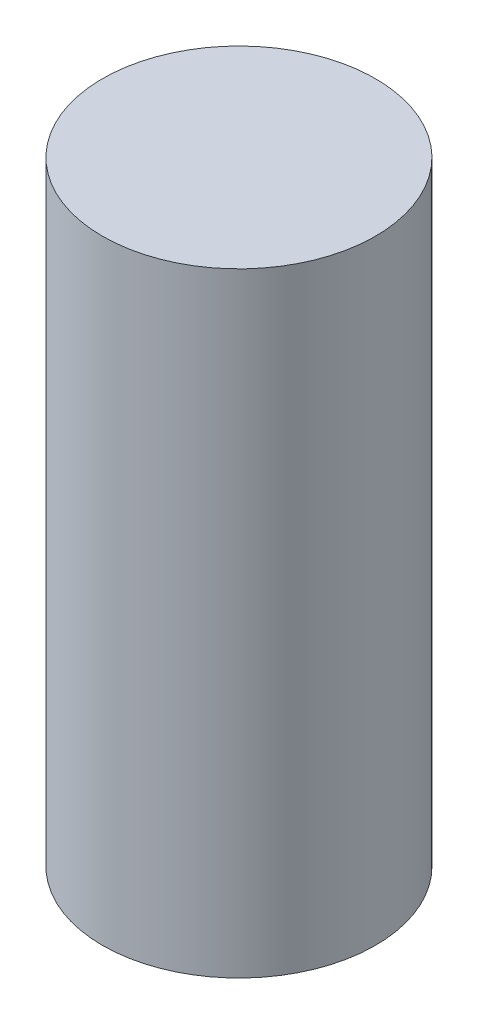
SolidWorks part; units mm, degrees
ref_plane "Front Plane" through (0, 0, 0) normal (0, 0, 1) x (1, 0, 0)
ref_plane "Top Plane" through (0, 0, 0) normal (0, 1, 0) x (1, 0, 0)
ref_plane "Right Plane" through (0, 0, 0) normal (1, 0, 0) x (0, 0, -1)
sketch "Sketch1" plane through (0, 0, 0) normal (0, 1, 0) x (1, 0, 0)
  circle A0 centre (0, 0) radius 5
  dimension "D1" = 10
extrude "Boss-Extrude1" add sketch "Sketch1" along normal blind 22.5
scale "Scale1" scale about centroid uniform scaling yes scale factor 0.66
